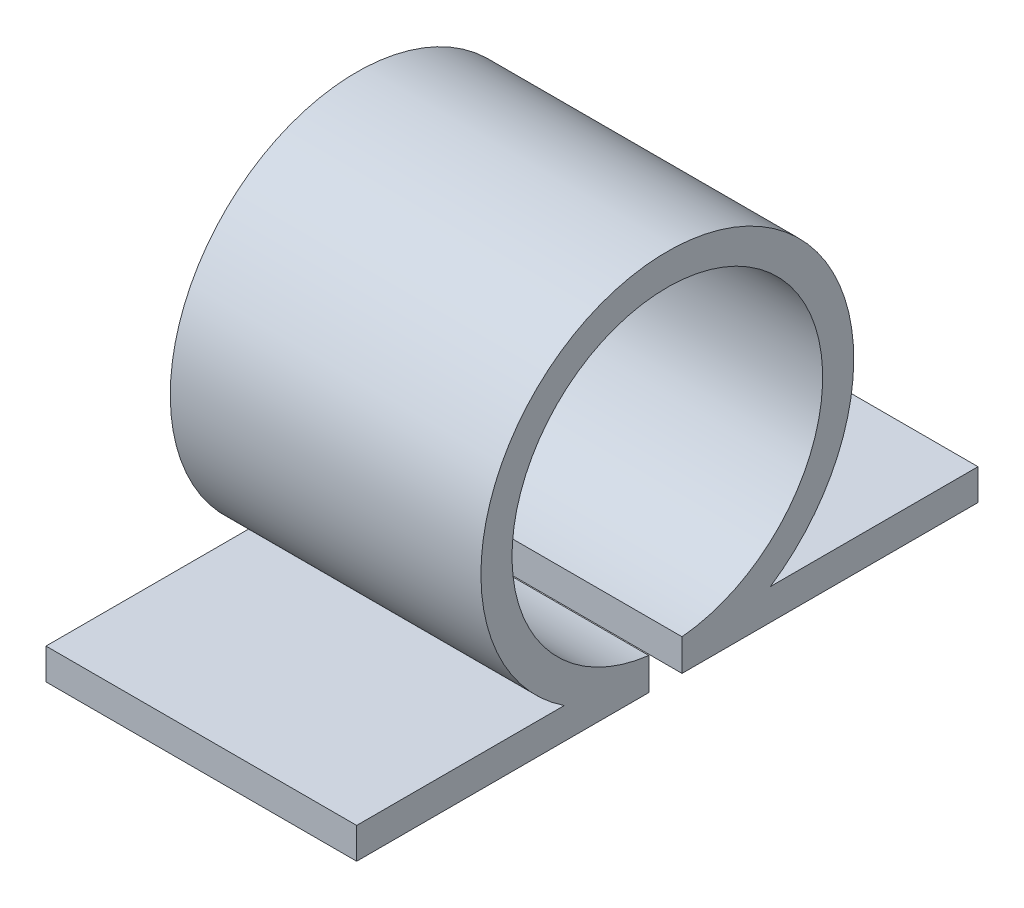
SolidWorks part; units mm, degrees
ref_plane "Front Plane" through (0, 0, 0) normal (0, 0, 1) x (1, 0, 0)
ref_plane "Top Plane" through (0, 0, 0) normal (0, 1, 0) x (1, 0, 0)
ref_plane "Right Plane" through (0, 0, 0) normal (1, 0, 0) x (0, 0, -1)
sketch "Sketch1" plane through (0, 0, 0) normal (1, 0, 0) x (0, 0, -1)
  line L0 (10, -5) -> (3.3166, -5)
  line L1 (-3.3166, -5) -> (-10, -5)
  line L2 (10, -6) -> (0.473, -6)
  line L3 (-10, -5) -> (-10, -6)
  line L4 (-10, -6) -> (-0.5971, -6)
  line L5 (10, -5) -> (10, -6)
  line L6 (-10, -5) -> (10, -6) construction
  line L7 (-10, -6) -> (10, -5) construction
  line L8 (-0.5971, -6) -> (-0.5971, -4.9642)
  line L9 (0.473, -6) -> (0.473, -4.9776)
  arc A0 (3.3166, -5) -> (-3.3166, -5) centre (0, 0) ccw
  arc A1 (0.473, -4.9776) -> (-0.5971, -4.9642) centre (0, 0) ccw
  point P0 (0, 0)
  point P7 (0, -5.5)
  dimension "D3" = 20
extrude "Boss-Extrude1" add sketch "Sketch1" along normal blind 10
